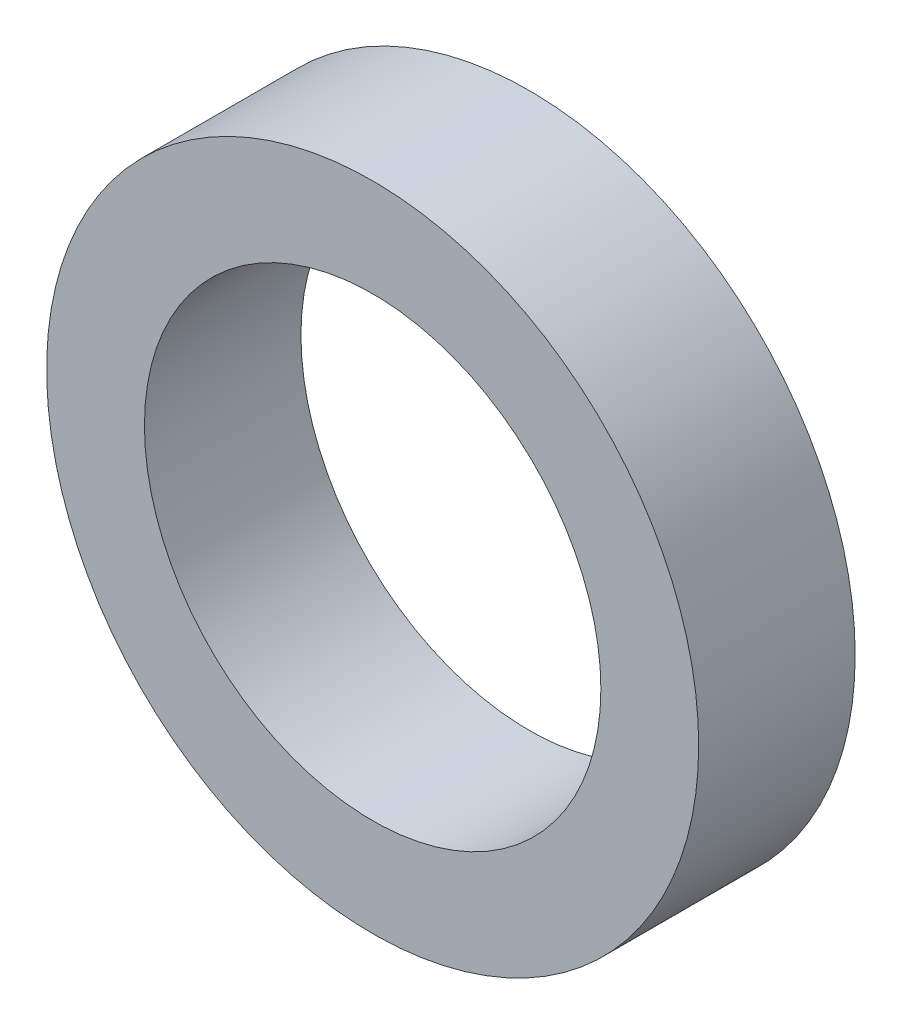
SolidWorks part; units mm, degrees
material "Ст 3 ГОСТ 380-2005"
ref_plane "Спереди" through (0, 0, 0) normal (0, 0, 1) x (1, 0, 0)
ref_plane "Сверху" through (0, 0, 0) normal (0, 1, 0) x (1, 0, 0)
ref_plane "Слева" through (0, 0, 0) normal (1, 0, 0) x (0, 0, -1)
sketch "Эскиз1" plane through (0, 0, 0) normal (0, 0, 1) x (1, 0, 0)
  circle A0 centre (0, 0) radius 8.75
  circle A1 centre (0, 0) radius 12.5
  dimension "D1" = 17.5
  dimension "D2" = 25
  dimension "D3" = 3.75
extrude "Вытянуть1" add sketch "Эскиз1" against normal blind 6
